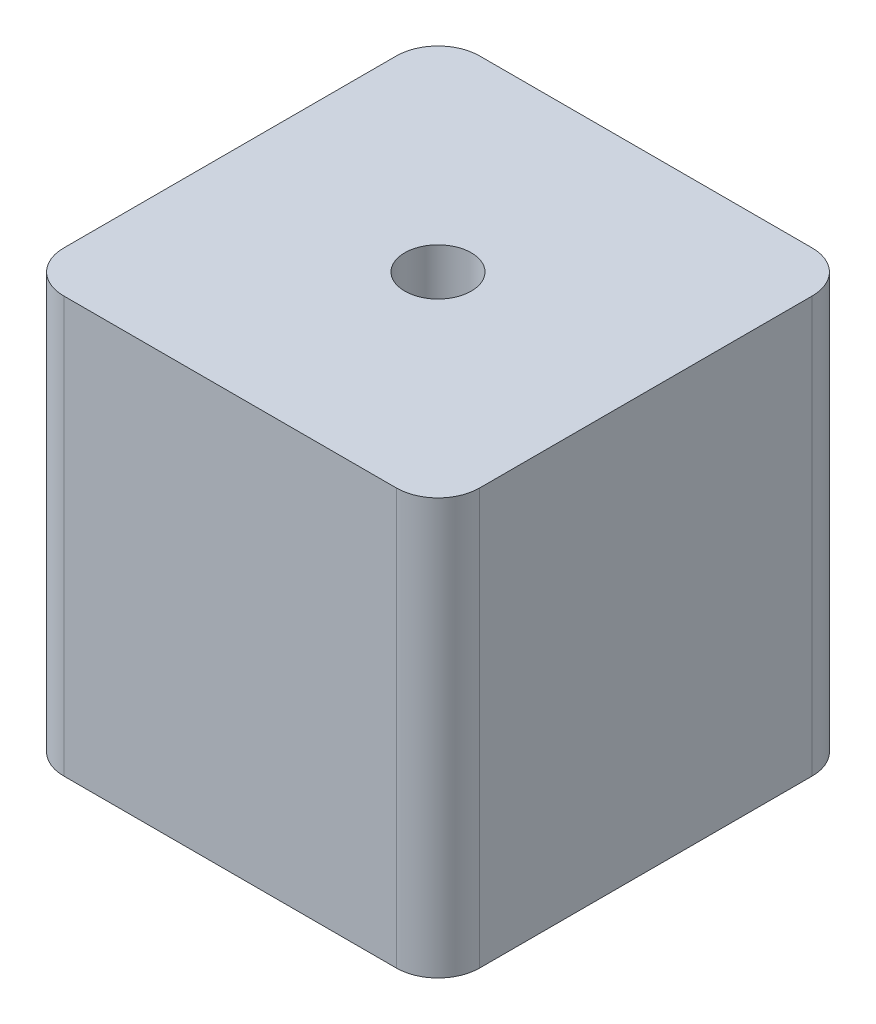
SolidWorks part; units mm, degrees
ref_plane "前视基准面" through (0, 0, 0) normal (0, 0, 1) x (1, 0, 0)
ref_plane "上视基准面" through (0, 0, 0) normal (0, 1, 0) x (1, 0, 0)
ref_plane "右视基准面" through (0, 0, 0) normal (1, 0, 0) x (0, 0, -1)
sketch "草图1" plane through (0, 0, 0) normal (0, 1, 0) x (1, 0, 0)
  line L1 (-10, 10) -> (10, 10)
  line L2 (-10, 10) -> (-10, -10)
  line L3 (-10, -10) -> (10, -10)
  line L4 (10, 10) -> (10, -10)
  line L5 (-10, 10) -> (10, -10) construction
  line L6 (-10, -10) -> (10, 10) construction
  circle A0 centre (0, 0) radius 1.6
  point P0 (0, 0)
  dimension "D3" = 3.2
  dimension "D1" = 20
  dimension "D2" = 20
extrude "凸台-拉伸1" add sketch "草图1" along normal blind 20
fillet "圆角1" radius 2 4 edges at (-10, 10, -10) (-10, 10, 10) (10, 10, 10) (10, 10, -10)
